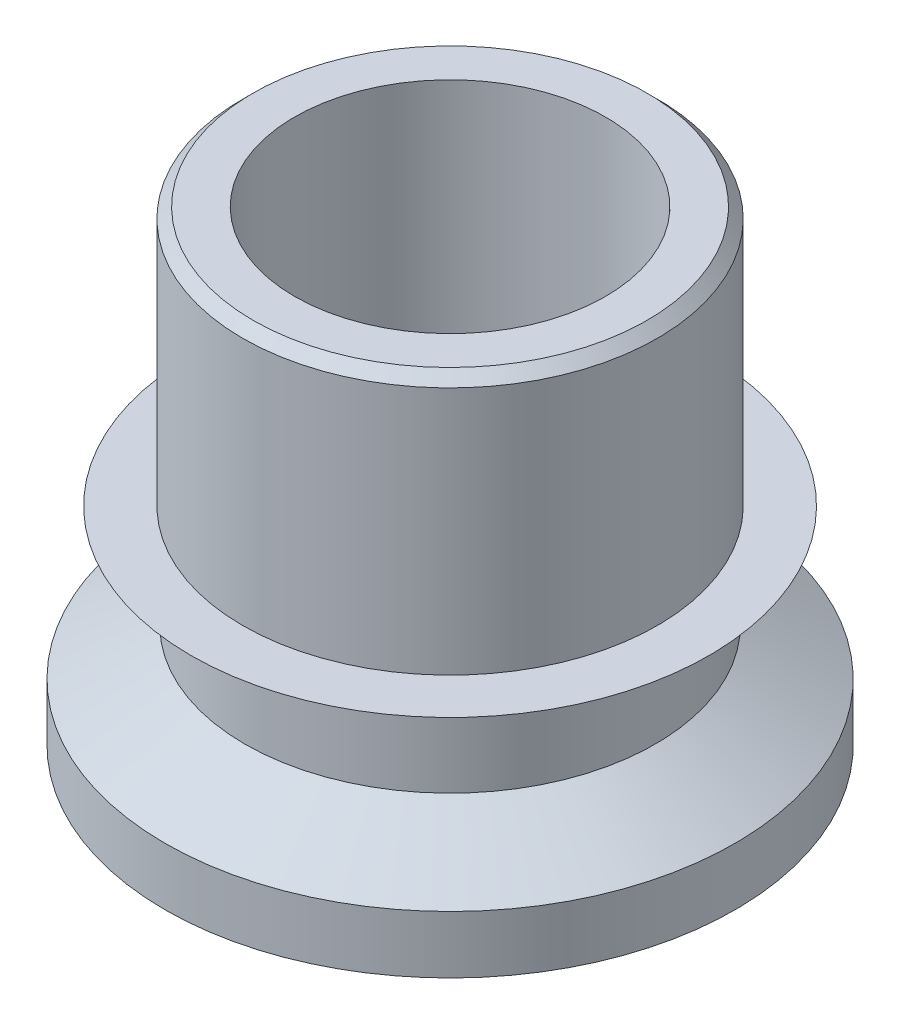
SolidWorks part; units mm, degrees
material "Titanium"
ref_plane "Front Plane" through (0, 0, 0) normal (0, 0, 1) x (1, 0, 0)
ref_plane "Top Plane" through (0, 0, 0) normal (0, 1, 0) x (1, 0, 0)
ref_plane "Right Plane" through (0, 0, 0) normal (1, 0, 0) x (0, 0, -1)
sketch "Sketch1" plane through (0, 0, 0) normal (0, 0, 1) x (1, 0, 0)
  line L0 (0, 0) -> (0, -50000) construction
  line L1 (-3, 7) -> (-3.8, 7)
  line L2 (-4, 6.8) -> (-4, 2)
  line L3 (-4, 2) -> (-5, 2)
  line L4 (-5, 2) -> (-3.9608, 1.4)
  line L5 (-3.9608, 1.4) -> (-3.9608, 0)
  line L6 (-3.9608, 0) -> (-5.5, -0.8887)
  line L7 (-5.5, -0.8887) -> (-5.5, -2)
  line L8 (-5.5, -2) -> (-3, -2)
  line L10 (-3.8, 7) -> (-4, 6.8)
  line L11 (-3, 7) -> (-3, -2)
  line L12 (-5.5, 0) -> (0, 0) construction
  point P4 (-4, 7)
  dimension "D1" = 6
  dimension "D2" = 11
  dimension "D4" = 30
  dimension "D5" = 30
  dimension "D6" = 2
  dimension "D7" = 4
  dimension "D8" = 10
  dimension "D9" = 9
  dimension "D10" = 8
  dimension "D11" = 1.4
revolve "Revolve1" add sketch "Sketch1" angle 360 about L0
